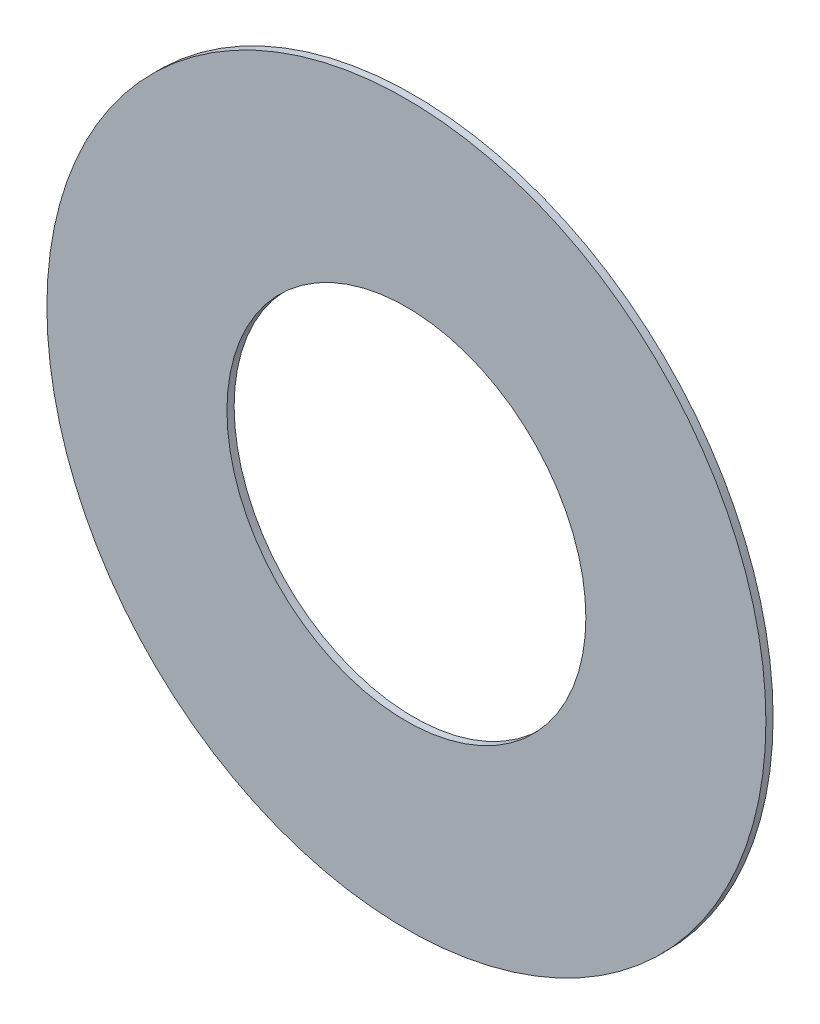
SolidWorks part; units mm, degrees
ref_plane "Front Plane" through (0, 0, 0) normal (0, 0, 1) x (1, 0, 0)
ref_plane "Top Plane" through (0, 0, 0) normal (0, 1, 0) x (1, 0, 0)
ref_plane "Right Plane" through (0, 0, 0) normal (1, 0, 0) x (0, 0, -1)
sketch "Sketch1" plane through (0, 0, 0) normal (0, 0, 1) x (1, 0, 0)
  circle A0 centre (0, 0) radius 39.624
  circle A1 centre (0, 0) radius 79.375
  dimension "D1" = 158.75
  dimension "D2" = 79.248
extrude "Boss-Extrude1" add sketch "Sketch1" along normal blind 1.5875
